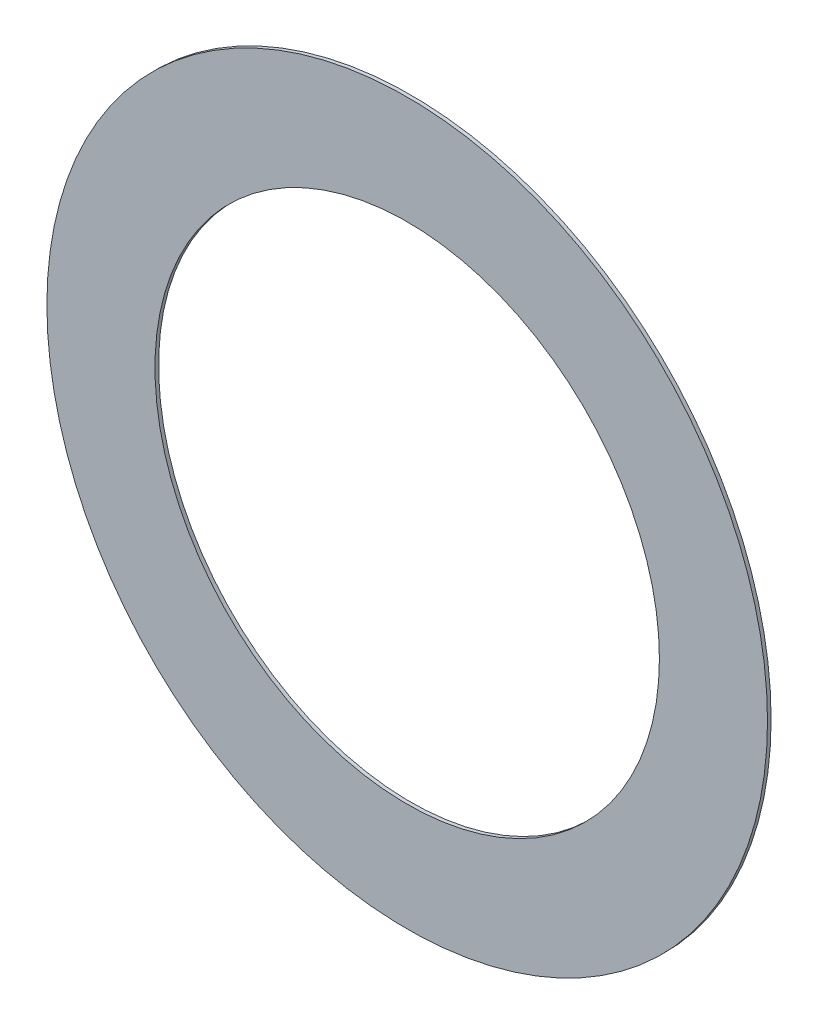
SolidWorks part; units mm, degrees
ref_plane "Front Plane" through (0, 0, 0) normal (0, 0, 1) x (1, 0, 0)
ref_plane "Top Plane" through (0, 0, 0) normal (0, 1, 0) x (1, 0, 0)
ref_plane "Right Plane" through (0, 0, 0) normal (1, 0, 0) x (0, 0, -1)
sketch "Sketch1" plane through (0, 0, 0) normal (0, 0, 1) x (1, 0, 0)
  line L0 (-10, 0) -> (10, 0) construction
  line L1 (0, -10) -> (0, 10) construction
  circle A0 centre (0, 0) radius 10
  circle A1 centre (0, 0) radius 7
  point P4 (0, 0)
  point P9 (0, 0)
  dimension "ID" = 14
  dimension "OD" = 20
sketch "Sketch2" plane through (0, 0, 0) normal (1, 0, 0) x (0, 0, -1)
  line L0 (0.05, 10) -> (-0.05, 10) construction
  line L1 (0, 10) -> (0, -10) construction
  point P4 (0, 10)
  dimension "Thickness" = 0.1
sketch "Sketch3" plane through (0, 0, 0) normal (0, 0, 1) x (1, 0, 0)
  line L0 (0, -10) -> (0, 10) construction
  circle A0 centre (0, 0) radius 10
  circle A1 centre (0, 0) radius 7
  circle A2 centre (0, 0) radius 7 construction
extrude "Boss-Extrude1" add sketch "Sketch3" along normal mid plane 0.1
equation "\"D1@Boss-Extrude1\" = \"Thickness@Sketch2\""
